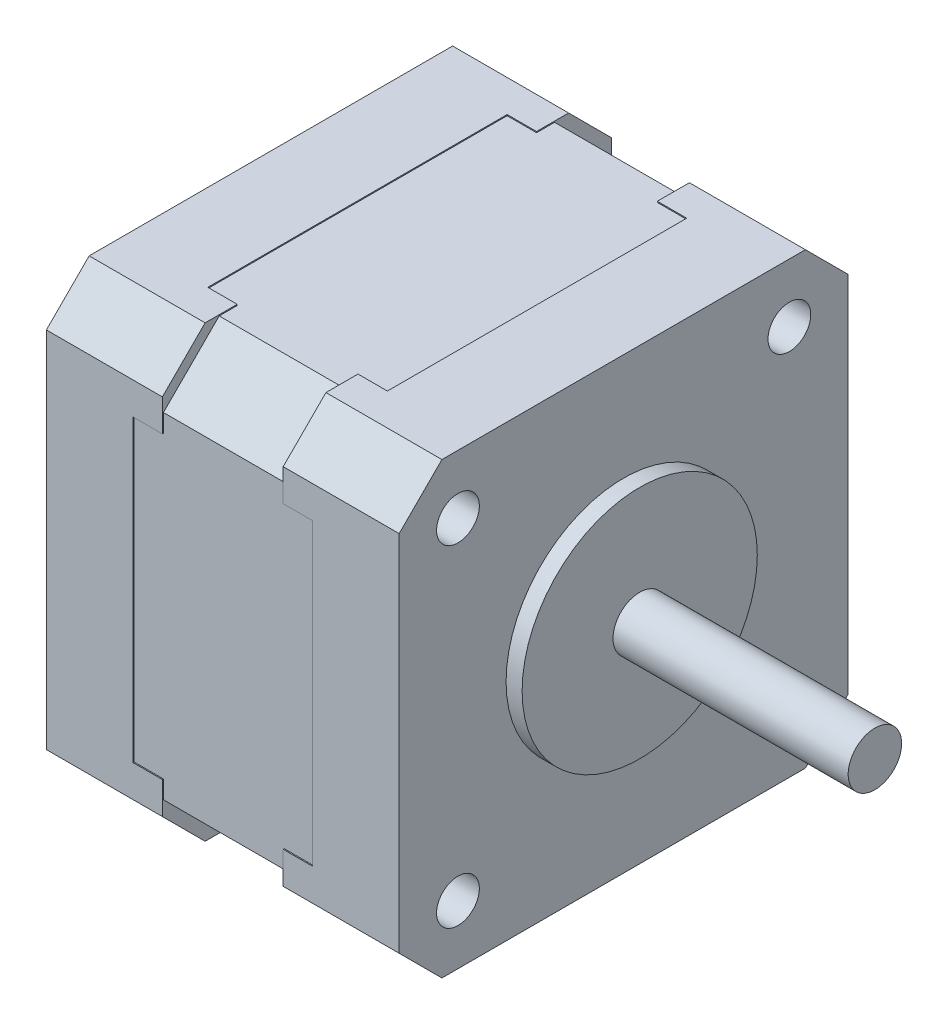
SolidWorks part; units mm, degrees
ref_plane "Alzado" through (0, 0, 0) normal (0, 0, 1) x (1, 0, 0)
ref_plane "Planta" through (0, 0, 0) normal (0, 1, 0) x (1, 0, 0)
ref_plane "Vista lateral" through (0, 0, 0) normal (1, 0, 0) x (0, 0, -1)
ref_plane "Plano1" through (-5.65, 0, 0) normal (-1, 0, 0) x (0, -1, 0)
sketch "Croquis1" plane through (-5.65, 0, 0) normal (-1, 0, 0) x (0, -1, 0)
  line L0 (20.9, -20.9) -> (20.9, 20.9)
  line L1 (20.9, 20.9) -> (-20.9, 20.9)
  line L2 (-20.9, 20.9) -> (-20.9, -20.9)
  line L3 (-20.9, -20.9) -> (20.9, -20.9)
extrude "Saliente-Extruir1" add sketch "Croquis1" against normal blind 11.3
sketch "Croquis2" plane through (5.65, 0, 0) normal (1, 0, 0) x (0, 0, -1)
  line L0 (21, 20.9) -> (21, -21)
  line L1 (21, -21) -> (-21, -21)
  line L2 (-21, -21) -> (-21, 20.9)
  line L3 (-21, 20.9) -> (21, 20.9)
extrude "Saliente-Extruir2" add sketch "Croquis2" along normal blind 10.85
sketch "Croquis3" plane through (0, 20.9, 0) normal (0, 1, 0) x (-1, 0, 0)
  line L0 (-5.65, -21) -> (-16.5, -21)
  line L1 (-16.5, -21) -> (-16.5, 21)
  line L2 (-16.5, 21) -> (-5.65, 21)
  line L3 (-5.65, 21) -> (-5.65, -21)
extrude "Saliente-Extruir3" add sketch "Croquis3" along normal blind 0.1
ref_plane "Plano2" through (-5.65, 0, 0) normal (1, 0, 0) x (0, 0, -1)
sketch "Croquis4" plane through (-5.65, 0, 0) normal (1, 0, 0) x (0, 0, -1)
  line L0 (21, 21) -> (-21, 21)
  line L1 (-21, 21) -> (-21, -21)
  line L2 (-21, -21) -> (21, -21)
  line L3 (21, -21) -> (21, 21)
extrude "Saliente-Extruir4" add sketch "Croquis4" against normal blind 10.85
ref_plane "Plano3" through (8.4, 0, 0) normal (1, 0, 0) x (0, 0, -1)
sketch "Croquis5" plane through (8.4, 0, 0) normal (1, 0, 0) x (0, 0, -1)
  line L0 (20.9, 14) -> (20.9, -14)
  line L1 (20.9, -14) -> (21, -14)
  line L2 (21, -14) -> (21, 14)
  line L3 (21, 14) -> (20.9, 14)
extrude "Cortar-Extruir1" cut sketch "Croquis5" against normal up to next
ref_plane "Plano4" through (-8.4, 0, 0) normal (-1, 0, 0) x (0, -1, 0)
sketch "Croquis6" plane through (-8.4, 0, 0) normal (-1, 0, 0) x (0, -1, 0)
  line L0 (-14, 21) -> (-14, 20.9)
  line L1 (-14, 20.9) -> (14, 20.9)
  line L2 (14, 20.9) -> (14, 21)
  line L3 (14, 21) -> (-14, 21)
extrude "Cortar-Extruir2" cut sketch "Croquis6" against normal up to next
sketch "Croquis7" plane through (0, -21, 0) normal (0, -1, 0) x (1, 0, 0)
  line L0 (8.4, -14) -> (8.4, 14)
  line L1 (8.4, 14) -> (5.65, 14)
  line L2 (5.65, 14) -> (5.65, -14)
  line L3 (5.65, -14) -> (8.4, -14)
extrude "Cortar-Extruir3" cut sketch "Croquis7" against normal blind 0.1
sketch "Croquis8" plane through (0, 0, 21) normal (0, 0, 1) x (1, 0, 0)
  line L0 (8.4, -14) -> (8.4, 14)
  line L1 (8.4, 14) -> (5.65, 14)
  line L2 (5.65, 14) -> (5.65, -14)
  line L3 (5.65, -14) -> (8.4, -14)
extrude "Cortar-Extruir4" cut sketch "Croquis8" against normal blind 0.1
sketch "Croquis9" plane through (5.65, 0, 0) normal (-1, 0, 0) x (0, 0, 1)
  line L0 (-14, 20.9) -> (14, 20.9)
  line L1 (14, 20.9) -> (14, 21)
  line L2 (14, 21) -> (-14, 21)
  line L3 (-14, 21) -> (-14, 20.9)
extrude "Cortar-Extruir5" cut sketch "Croquis9" against normal blind 2.75
sketch "Croquis10" plane through (0, -21, 0) normal (0, -1, 0) x (1, 0, 0)
  line L0 (-5.65, -14) -> (-5.65, 14)
  line L1 (-5.65, 14) -> (-8.4, 14)
  line L2 (-8.4, 14) -> (-8.4, -14)
  line L3 (-8.4, -14) -> (-5.65, -14)
extrude "Cortar-Extruir6" cut sketch "Croquis10" against normal blind 0.1
sketch "Croquis11" plane through (0, 0, -21) normal (0, 0, -1) x (-1, 0, 0)
  line L0 (5.65, 14) -> (5.65, -14)
  line L1 (5.65, -14) -> (8.4, -14)
  line L2 (8.4, -14) -> (8.4, 14)
  line L3 (8.4, 14) -> (5.65, 14)
extrude "Cortar-Extruir7" cut sketch "Croquis11" against normal blind 0.1
sketch "Croquis12" plane through (0, 21, 0) normal (0, 1, 0) x (-1, 0, 0)
  line L0 (5.65, 14) -> (5.65, -14)
  line L1 (5.65, -14) -> (8.4, -14)
  line L2 (8.4, -14) -> (8.4, 14)
  line L3 (8.4, 14) -> (5.65, 14)
extrude "Cortar-Extruir8" cut sketch "Croquis12" against normal blind 0.1
sketch "Croquis15" plane through (0, 0, 0) normal (0, 0, 1) x (1, 0, 0)
  line L0 (15.5, 11) -> (15.5, 0)
  line L1 (15.5, 0) -> (40, 0)
  line L2 (40, 0) -> (40, 2.5)
  line L3 (40, 2.5) -> (18, 2.5)
  line L4 (18, 2.5) -> (18, 11)
  line L5 (18, 11) -> (15.5, 11)
  line L6 (15.5, 0) -> (40, 0) construction
revolve "Revolución1" add sketch "Croquis15" angle 360 about L6
chamfer "Chaflán1" distance 5.2142 angle 45 4 edges at (0, -20.9, -20.9) (0, -20.9, 20.9)
chamfer "Chaflán2" distance 4 angle 45 8 edges at (-11.075, 21, -21) (-11.075, -21, 21) (11.075, -21, -21) (11.075, 21, -21) (-11.075, 21, 21) (11.075, 21, 21) (-11.075, -21, -21) (11.075, -21, 21)
ref_plane "Plano5" through (12.45, 0, 0) normal (1, 0, 0) x (0, 0, -1)
sketch "Croquis18" plane through (12.45, 0, 0) normal (1, 0, 0) x (0, 0, -1)
  line L0 (0, 0) -> (0, 2.3727) construction
  line L1 (0, 36.4567) -> (0, 0) construction
  line L2 (0, 0) -> (37.7341, 0) construction
  line L4 (15.5, -15.5) -> (-15.5, -15.5) construction
  line L5 (15.5, -15.5) -> (15.5, 15.5) construction
  line L6 (15.5, 15.5) -> (-15.5, 15.5) construction
  line L7 (-15.5, -15.5) -> (-15.5, 15.5) construction
  line L8 (15.5, -15.5) -> (-15.5, 15.5) construction
  line L9 (15.5, 15.5) -> (-15.5, -15.5) construction
  circle A0 centre (-15.5, 15.5) radius 2
  circle A1 centre (15.5, 15.5) radius 2
  circle A2 centre (15.5, -15.5) radius 2
  circle A3 centre (-15.5, -15.5) radius 2
  dimension "D3" = 4
  dimension "D1" = 15.5
  dimension "D2" = 15.5
extrude "Cortar-Extruir10" cut sketch "Croquis18" against normal blind 3 and the other way blind 6
